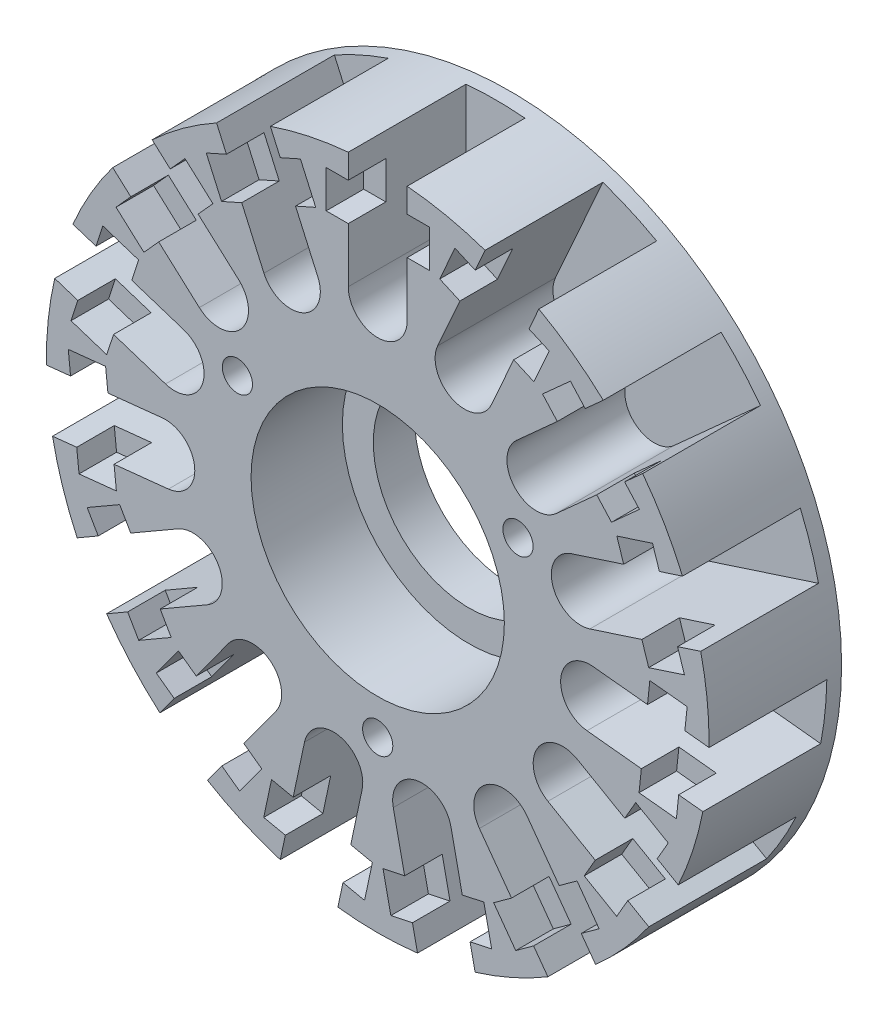
SolidWorks part; units mm, degrees
ref_plane "Front Plane" through (0, 0, 0) normal (0, 0, 1) x (1, 0, 0)
ref_plane "Top Plane" through (0, 0, 0) normal (0, 1, 0) x (1, 0, 0)
ref_plane "Right Plane" through (0, 0, 0) normal (1, 0, 0) x (0, 0, -1)
sketch "Sketch1" plane through (0, 0, 0) normal (0, 1, 0) x (1, 0, 0)
  line L0 (22.5, 0) -> (0, 0)
  line L1 (0, 0) -> (0, -9)
  line L2 (0, -9) -> (22.5, -9)
  line L3 (22.5, -9) -> (22.5, 0)
  line L4 (0, 0) -> (0, -9) construction
revolve "Revolve1" add sketch "Sketch1" angle 360 about L4
sketch "Sketch2" plane through (0, 0, 9) normal (0, 0, 1) x (1, 0, 0)
  line L0 (-2, 22.4109) -> (-2, 14.5)
  line L1 (2, 14.5) -> (2, 22.4109)
  arc A0 (-2, 14.5) -> (2, 14.5) centre (0, 14.5) ccw
  arc A1 (2, 22.4109) -> (-2, 22.4109) centre (0, 0) ccw
extrude "Cut-Extrude1" cut sketch "Sketch2" against normal blind 8
sketch "Sketch3" plane through (2, 0, 0) normal (-1, 0, 0) x (0, 0, 1)
  line L0 (9, 20.7609) -> (6.45, 20.7609)
  line L1 (6.45, 20.7609) -> (6.45, 18.2109)
  line L2 (6.45, 18.2109) -> (9, 18.2109)
  line L3 (9, 18.2109) -> (9, 20.7609)
  line L4 (1, 22.4109) -> (9, 22.4109) construction
  line L5 (9, -22.5) -> (9, 22.4109) construction
  dimension "D1" = 1.65
  dimension "D2" = 0
  dimension "D3" = 2.55
extrude "Cut-Extrude2" cut sketch "Sketch3" against normal blind 1.5
sketch "Sketch4" plane through (-2, 0, 0) normal (1, 0, 0) x (0, 0, -1)
  line L0 (-9, 18.2109) -> (-6.45, 18.2109)
  line L1 (-6.45, 18.2109) -> (-6.45, 20.7609)
  line L2 (-6.45, 20.7609) -> (-9, 20.7609)
  line L3 (-9, 20.7609) -> (-9, 18.2109)
  line L4 (-1, 22.4109) -> (-9, 22.4109) construction
  dimension "D1" = 1.65
  dimension "D2" = 2.55
  dimension "D3" = 2.55
extrude "Cut-Extrude3" cut sketch "Sketch4" against normal blind 1.5
hole_wizard "Ø2.05 (2.05) Diameter Hole1" positions "Sketch48" profile "Sketch47" hole size "Ø2.05" standard "ANSI Metric"
sketch "Sketch48" plane through (0, 0, 9) normal (0, 0, 1) x (1, 0, 0)
  point P0 (9.5263, 5.5)
  point P1 (0, -11)
  point P2 (-9.5263, 5.5)
sketch "Sketch47" plane through (9.5263, 5.5, 9) normal (1, 0, 0) x (0, -1, 0)
  line L0 (0, 0) -> (0, 8.6159)
  line L1 (0, 8.6159) -> (1.025, 8)
  line L2 (1.025, 8) -> (1.025, 0)
  line L5 (1.025, 0) -> (0, 0)
  line L10 (0, 8.6159) -> (-1.025, 8) construction
  line L11 (0, -6.35) -> (0, 107.95) construction
  dimension "Hole Dia." = 2.05
  dimension "Hole Depth" = 8
  dimension "Drill Angle" = 118
hole_wizard "CBORE for M12 Hex Head Bolt1" positions "Sketch50" profile "Sketch49" counterbore size "M12" standard "ANSI Metric"
sketch "Sketch50" plane through (0, 0, 9) normal (0, 0, 1) x (1, 0, 0)
  point P0 (0, 0)
sketch "Sketch49" plane through (0, 0, 9) normal (1, 0, 0) x (0, -1, 0)
  line L0 (0, 0) -> (0, 9)
  line L1 (0, 9) -> (6.5, 9)
  line L3 (6.5, 9) -> (6.5, 6.2)
  line L4 (6.5, 6.2) -> (8.6, 6.2)
  line L5 (8.6, 6.2) -> (8.6, 0)
  line L7 (8.6, 0) -> (0, 0)
  line L11 (0, -6.35) -> (0, 107.95) construction
  dimension "Thru Hole Dia." = 13
  dimension "Thru Hole Depth" = 9
  dimension "C'Bore Dia." = 17.2
  dimension "C'Bore Depth" = 6.2
hole_wizard "Ø2.5 (2.5) Diameter Hole1" positions "Sketch52" profile "Sketch51" hole size "Ø2.5" standard "ANSI Metric"
sketch "Sketch52" plane through (0, 0, 0) normal (0, 0, -1) x (-1, 0, 0)
  point P0 (16.8875, 9.75)
  point P1 (-16.8875, 9.75)
  point P2 (0, -19.5)
sketch "Sketch51" plane through (-16.8875, 9.75, 0) normal (1, 0, 0) x (0, 1, 0)
  line L0 (0, 0) -> (0, 5.7511)
  line L1 (0, 5.7511) -> (1.25, 5)
  line L2 (1.25, 5) -> (1.25, 0)
  line L5 (1.25, 0) -> (0, 0)
  line L10 (0, 5.7511) -> (-1.25, 5) construction
  line L11 (0, -6.35) -> (0, 107.95) construction
  dimension "Hole Dia." = 2.5
  dimension "Hole Depth" = 5
  dimension "Drill Angle" = 118
pattern_circular "CirPattern1" count 15 over 360 about axis through (0, 0, 0) along (0, 0, 1) of "Cut-Extrude1", "Cut-Extrude3", "Cut-Extrude2"
